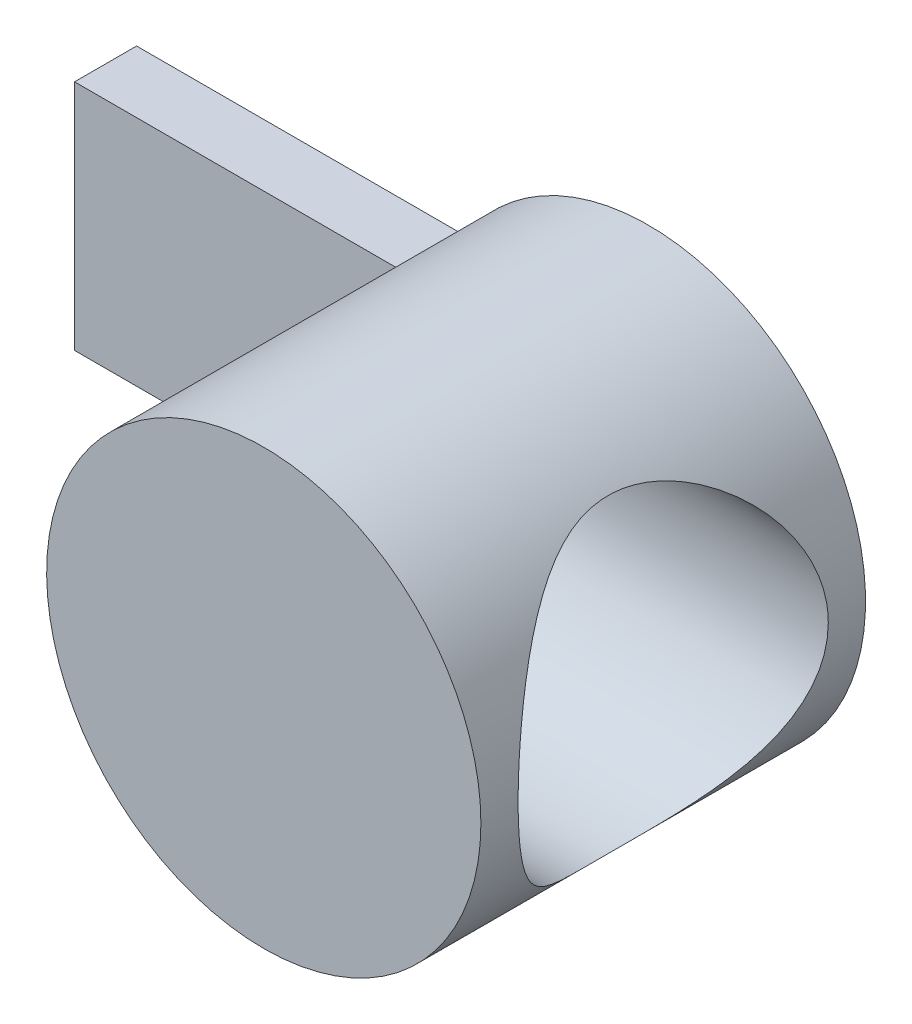
SolidWorks part; units mm, degrees
material "ЦА4М3 ГОСТ 25140-93"
ref_plane "Спереди" through (0, 0, 0) normal (0, 0, 1) x (1, 0, 0)
ref_plane "Сверху" through (0, 0, 0) normal (0, 1, 0) x (1, 0, 0)
ref_plane "Справа" through (0, 0, 0) normal (1, 0, 0) x (0, 0, -1)
sketch "Эскиз1" plane through (0, 0, 0) normal (0, 0, 1) x (1, 0, 0)
  circle A0 centre (0, 0) radius 7
  dimension "D1" = 7
extrude "Бобышка-Вытянуть1" add sketch "Эскиз1" along normal blind 12.4
sketch "Эскиз2" plane through (0, 0, 0) normal (0, 0, 1) x (1, 0, 0)
  line L1 (-5.9108, 3.75) -> (-16.5, 3.75)
  line L2 (-5.9108, 3.75) -> (-5.9108, -3.75)
  line L3 (-5.9108, -3.75) -> (-16.5, -3.75)
  line L4 (-16.5, 3.75) -> (-16.5, -3.75)
  circle A0 centre (0, 0) radius 7 construction
  dimension "D1" = 23.5
  dimension "D2" = 7.5
extrude "Бобышка-Вытянуть2" add sketch "Эскиз2" along normal blind 2
sketch "Эскиз3" plane through (0, 0, 0) normal (1, 0, 0) x (0, 0, -1)
  line L0 (-6.2, 7) -> (-6.2, 0) construction
  line L1 (0, 7) -> (-12.4, 7) construction
  circle A0 centre (-6.2, 0) radius 5
  dimension "D1" = 10
extrude "Вырез-Вытянуть1" cut sketch "Эскиз3" along normal through all and the other way blind 1.5
sketch "Эскиз4" plane through (-1.5, 0, 0) normal (1, 0, 0) x (0, 0, -1)
  circle A0 centre (-6.2, 0) radius 3.1
  dimension "D1" = 6.2
extrude "Вырез-Вытянуть2" cut sketch "Эскиз4" against normal through all
